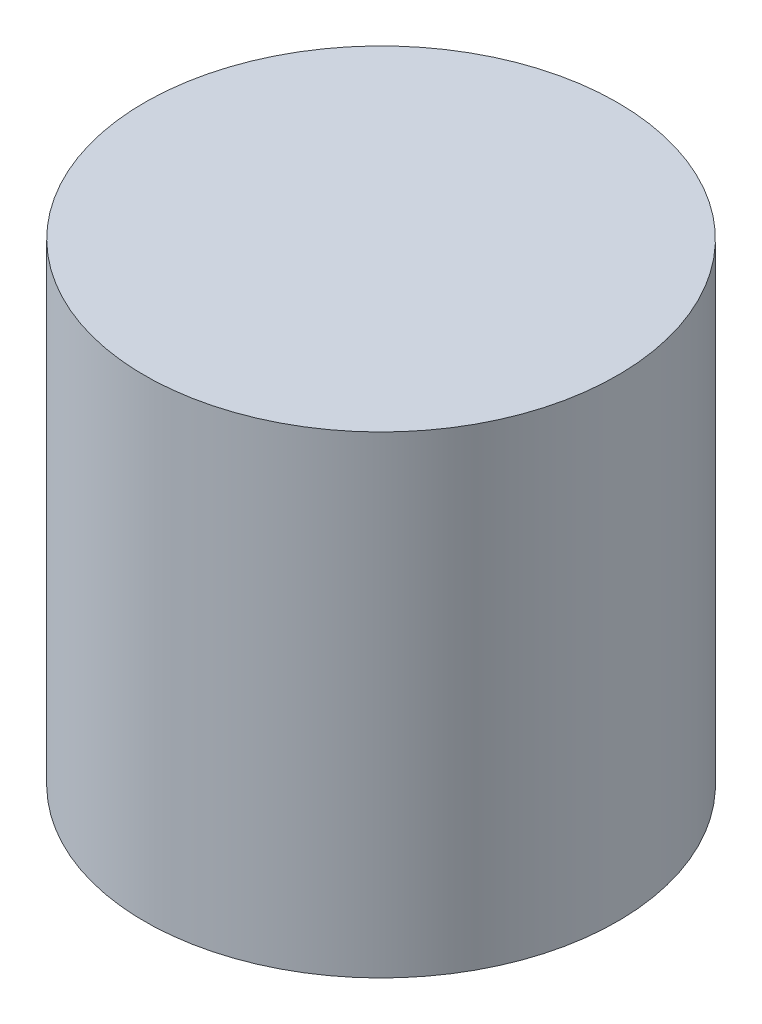
SolidWorks part; units mm, degrees
ref_plane "Front Plane" through (0, 0, 0) normal (0, 0, 1) x (1, 0, 0)
ref_plane "Top Plane" through (0, 0, 0) normal (0, 1, 0) x (1, 0, 0)
ref_plane "Right Plane" through (0, 0, 0) normal (1, 0, 0) x (0, 0, -1)
sketch "Sketch1" plane through (0, 0, 0) normal (1, 0, 0) x (0, 0, -1)
  line L0 (-69.7123, -111.3858) -> (-18.9123, -111.3858)
  dimension "D1" = 50.8
  dimension "D2" = 15.24
  dimension "D3" = 21.209
ref_plane "Plane1" through (0, -111.3858, 0) normal (0, -1, 0) x (1, 0, 0)
sketch "Sketch2" plane through (0, -111.3858, 0) normal (0, -1, 0) x (1, 0, 0)
  line L0 (0, 44.3123) -> (152.4515, 44.3123) construction
  line L1 (0, 69.7123) -> (0, 18.9123) construction
  circle A0 centre (70.6453, 44.3123) radius 25.4
  dimension "D1" = 50.8
  dimension "D2" = 70.6453
extrude "Boss-Extrude1" add sketch "Sketch2" along normal blind 50.8
